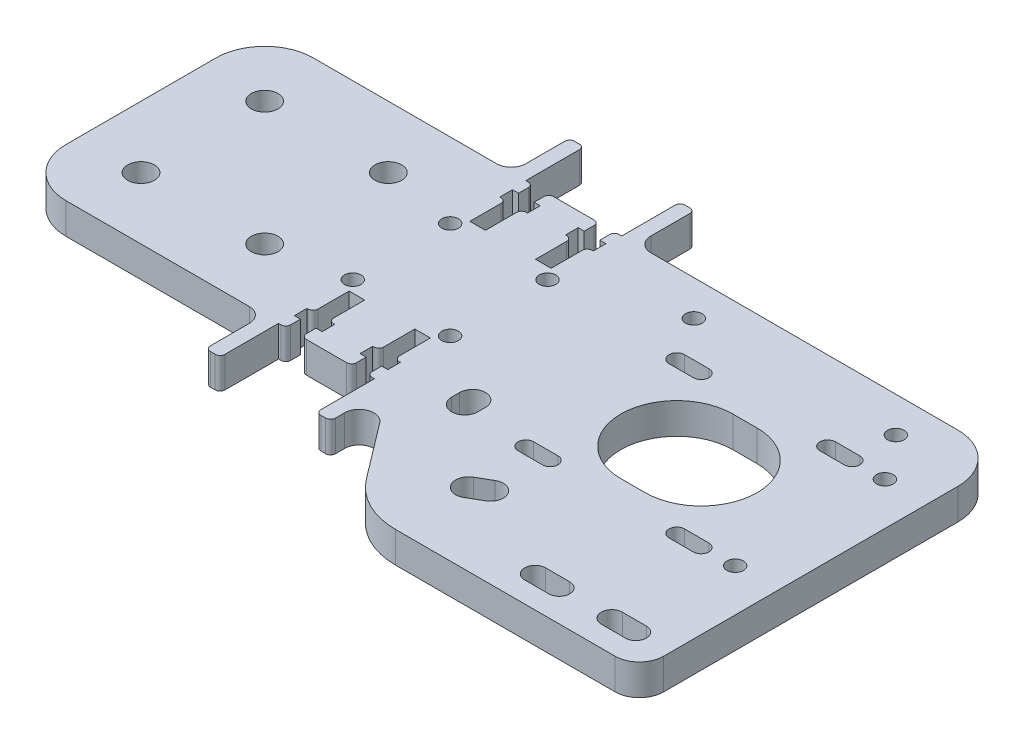
SolidWorks part; units mm, degrees
material "6061-T6 (SS)"
ref_plane "Front" through (0, 0, 0) normal (0, 0, 1) x (1, 0, 0)
ref_plane "Top" through (0, 0, 0) normal (0, 1, 0) x (1, 0, 0)
ref_plane "Right" through (0, 0, 0) normal (1, 0, 0) x (0, 0, -1)
sketch "Sketch1" plane through (0, 0, 0) normal (0, 1, 0) x (1, 0, 0)
  line L0 (0, 0) -> (114.3212, 0) construction
  line L1 (38.1, -25.4) -> (-38.1, -25.4)
  line L2 (38.1, -25.4) -> (38.1, 25.4) construction
  line L3 (38.1, 25.4) -> (-38.1, 25.4)
  line L4 (-38.1, -25.4) -> (-38.1, 25.4)
  line L5 (38.1, -25.4) -> (-38.1, 25.4) construction
  line L6 (38.1, 25.4) -> (-38.1, -25.4) construction
  line L7 (25.4, 25.4) -> (25.4, -25.4) construction
  line L8 (-25.4, 25.4) -> (-25.4, -25.4) construction
  line L9 (0, -25.4) -> (0, 25.4) construction
  line L10 (0, 0) -> (-38.1, 0) construction
  line L11 (-25.4, 0) -> (-25.4, 25.4) construction
  line L12 (-25.4, 12.7) -> (0, 12.7) construction
  line L13 (25.4, -41.4) -> (114.3212, -41.4) construction
  line L14 (99.3212, -27.36) -> (57.3212, -27.36) construction
  line L15 (99.3212, -27.36) -> (99.3212, 14.64) construction
  line L16 (99.3212, 14.64) -> (57.3212, 14.64) construction
  line L17 (57.3212, -27.36) -> (57.3212, 14.64) construction
  line L18 (99.3212, -27.36) -> (57.3212, 14.64) construction
  line L19 (99.3212, 14.64) -> (57.3212, -27.36) construction
  line L20 (93.8212, -21.86) -> (62.8212, -21.86) construction
  line L21 (93.8212, -21.86) -> (93.8212, 9.14) construction
  line L22 (93.8212, 9.14) -> (62.8212, 9.14) construction
  line L23 (62.8212, -21.86) -> (62.8212, 9.14) construction
  line L24 (93.8212, -21.86) -> (62.8212, 9.14) construction
  line L25 (93.8212, 9.14) -> (62.8212, -21.86) construction
  line L26 (114.3212, -41.4) -> (114.3212, 0) construction
  line L27 (49.1, -12.72) -> (78.3212, -12.72) construction
  line L28 (47.8664, -25.3192) -> (65.4755, -28.8008) construction
  line L29 (38.1, -25.4) -> (52.2919, -44.1062)
  line L30 (78.3212, 0) -> (0, 0) construction
  line L31 (35.4, 10) -> (15.4, 10) construction
  line L32 (64.2419, -50.04) -> (114.3212, -50.04)
  line L33 (114.3212, -50.04) -> (114.3212, 25.4)
  line L34 (114.3212, 25.4) -> (38.1, 25.4)
  line L35 (49.1, -19.08) -> (49.1, -20.72) construction
  line L36 (64.2419, -35.04) -> (67.0783, -33.4) construction
  line L37 (64.2419, -35.04) -> (64.2419, -50.04) construction
  circle A0 centre (-25.4, 12.7) radius 2.5 construction
  circle A1 centre (0, 12.7) radius 2.5 construction
  circle A2 centre (-25.4, -12.7) radius 2.5 construction
  circle A3 centre (0, -12.7) radius 2.5 construction
  circle A4 centre (78.3212, -6.36) radius 6.36 construction
  circle A5 centre (78.3212, -6.36) radius 11 construction
  circle A6 centre (62.8212, 9.14) radius 1.5 construction
  circle A7 centre (93.8212, 9.14) radius 1.5 construction
  circle A8 centre (93.8212, -21.86) radius 1.5 construction
  circle A9 centre (62.8212, -21.86) radius 1.5 construction
  circle A10 centre (64.2419, -35.04) radius 6.36 construction
  circle A11 centre (64.2419, -35.04) radius 11 construction
  circle A12 centre (49.1, -19.08) radius 6.36 construction
  circle A13 centre (49.1, -19.08) radius 11 construction
  circle A14 centre (62.8212, -21.86) radius 3 construction
  circle A15 centre (35.4, 10) radius 1.5 construction
  circle A16 centre (15.4, 10) radius 1.5 construction
  circle A17 centre (35.4, -10) radius 1.5 construction
  circle A18 centre (15.4, -10) radius 1.5 construction
  circle A19 centre (49.1, -19.08) radius 2.5 construction
  circle A20 centre (64.2419, -35.04) radius 2.5 construction
  circle A21 centre (78.3212, -6.36) radius 11 construction
  arc A22 (52.2919, -44.1062) -> (64.2419, -50.04) centre (64.2419, -35.04) ccw
  circle A23 centre (49.1, -20.72) radius 8 construction
  circle A24 centre (49.1, -20.72) radius 11 construction
  circle A25 centre (67.0783, -33.4) radius 8 construction
  circle A26 centre (67.0783, -33.4) radius 11 construction
  point P0 (0, 0)
  point P54 (25.4, 10)
  dimension "D6" = 5
  dimension "D7" = 12.72
  dimension "D9" = 22
  dimension "D11" = 3
  dimension "D12" = 16
  dimension "D13" = 6
  dimension "D16" = 3
  dimension "D17" = 5
  dimension "D18" = 22
  dimension "D20" = 16
  dimension "D21" = 4
  dimension "D1" = 50.8
  dimension "D2" = 76.2
  dimension "D3" = 12.7
  dimension "D4" = 12.7
  dimension "D5" = 25.4
  dimension "D8" = 42
  dimension "D10" = 31
  dimension "D14" = 20
  dimension "D15" = 10
  dimension "D19" = 15
extrude "Boss-Extrude1" add sketch "Sketch1" along normal blind 6.35
hole_wizard "M5 Clearance Hole1" positions "Sketch3" profile "Sketch2" hole size "M5" standard "ISO" end condition through all
sketch "Sketch3" plane through (0, 6.35, 0) normal (0, 1, 0) x (1, 0, 0)
  point P0 (-25.4, 12.7)
  point P3 (0, 12.7)
  point P6 (0, -12.7)
  point P9 (-25.4, -12.7)
sketch "Sketch2" plane through (-25.4, 6.35, -12.7) normal (1, 0, 0) x (0, 0, 1)
  line L0 (0, 0) -> (0, 6.35)
  line L1 (0, 6.35) -> (2.75, 6.35)
  line L2 (2.75, 6.35) -> (2.75, 0)
  line L5 (2.75, 0) -> (0, 0)
  line L11 (0, -6.35) -> (0, 107.95) construction
  dimension "Thru Hole Dia." = 5.5
  dimension "Thru Hole Depth" = 6.35
hole_wizard "M3 Clearance Hole1" positions "Sketch5" profile "Sketch4" hole size "M3" standard "ISO" end condition through all
sketch "Sketch5" plane through (0, 6.35, 0) normal (0, 1, 0) x (1, 0, 0)
  point P0 (15.4, 10)
  point P3 (35.4, 10)
  point P6 (35.4, -10)
  point P9 (15.4, -10)
sketch "Sketch4" plane through (15.4, 6.35, -10) normal (1, 0, 0) x (0, 0, 1)
  line L0 (0, 0) -> (0, 6.35)
  line L1 (0, 6.35) -> (1.7, 6.35)
  line L2 (1.7, 6.35) -> (1.7, 0)
  line L5 (1.7, 0) -> (0, 0)
  line L11 (0, -6.35) -> (0, 107.95) construction
  dimension "Thru Hole Dia." = 3.4
  dimension "Thru Hole Depth" = 6.35
sketch "Sketch6" plane through (0, 6.35, 0) normal (0, 1, 0) x (1, 0, 0)
  line L0 (62.8212, 9.14) -> (67.8212, 9.14) construction
  line L1 (93.8212, 9.14) -> (62.8212, 9.14) construction
  line L2 (62.8212, -21.86) -> (67.8212, -21.86) construction
  line L3 (93.8212, -21.86) -> (62.8212, -21.86) construction
  line L4 (93.8212, -21.86) -> (98.8212, -21.86) construction
  line L5 (93.8212, 9.14) -> (98.8212, 9.14) construction
  line L6 (62.8212, 7.54) -> (67.8212, 7.54)
  line L7 (62.8212, -23.46) -> (67.8212, -23.46)
  line L8 (93.8212, -23.46) -> (98.8212, -23.46)
  line L9 (93.8212, 7.54) -> (98.8212, 7.54)
  line L10 (62.8212, 10.74) -> (67.8212, 10.74)
  line L11 (62.8212, -20.26) -> (67.8212, -20.26)
  line L12 (93.8212, -20.26) -> (98.8212, -20.26)
  line L13 (93.8212, 10.74) -> (98.8212, 10.74)
  line L14 (78.3212, -6.36) -> (83.3212, -6.36) construction
  line L15 (99.3212, 14.64) -> (57.3212, -27.36) construction
  line L16 (78.3212, -17.86) -> (83.3212, -17.86)
  line L17 (78.3212, 5.14) -> (83.3212, 5.14)
  arc A0 (62.8212, 7.54) -> (62.8212, 10.74) centre (62.8212, 9.14) cw
  arc A1 (67.8212, 7.54) -> (67.8212, 10.74) centre (67.8212, 9.14) ccw
  arc A2 (62.8212, -23.46) -> (62.8212, -20.26) centre (62.8212, -21.86) cw
  arc A3 (67.8212, -23.46) -> (67.8212, -20.26) centre (67.8212, -21.86) ccw
  arc A4 (93.8212, -23.46) -> (93.8212, -20.26) centre (93.8212, -21.86) cw
  arc A5 (98.8212, -23.46) -> (98.8212, -20.26) centre (98.8212, -21.86) ccw
  arc A6 (93.8212, 7.54) -> (93.8212, 10.74) centre (93.8212, 9.14) cw
  arc A7 (98.8212, 7.54) -> (98.8212, 10.74) centre (98.8212, 9.14) ccw
  arc A8 (78.3212, -17.86) -> (78.3212, 5.14) centre (78.3212, -6.36) cw
  arc A9 (83.3212, -17.86) -> (83.3212, 5.14) centre (83.3212, -6.36) ccw
  dimension "D1" = 5
  dimension "D2" = 1.6
  dimension "D3" = 1.6
  dimension "D4" = 11.5
  dimension "D5" = 11.5
extrude "Cut-Extrude1" cut sketch "Sketch6" against normal through all
sketch "Sketch7" plane through (0, 6.35, 0) normal (0, 1, 0) x (1, 0, 0)
  line L0 (49.1, -19.08) -> (49.1, -20.72) construction
  line L1 (67.0783, -33.4) -> (64.2419, -35.04) construction
  line L2 (65.7518, -31.1059) -> (62.9155, -32.7459)
  line L3 (46.45, -19.08) -> (46.45, -20.72)
  line L4 (68.4047, -35.6941) -> (65.5684, -37.3341)
  line L5 (51.75, -19.08) -> (51.75, -20.72)
  arc A0 (65.7518, -31.1059) -> (68.4047, -35.6941) centre (67.0783, -33.4) cw
  arc A1 (62.9155, -32.7459) -> (65.5684, -37.3341) centre (64.2419, -35.04) ccw
  arc A2 (46.45, -19.08) -> (51.75, -19.08) centre (49.1, -19.08) cw
  arc A3 (46.45, -20.72) -> (51.75, -20.72) centre (49.1, -20.72) ccw
  dimension "D1" = 2.65
  dimension "D2" = 2.65
extrude "Cut-Extrude2" cut sketch "Sketch7" against normal through all
fillet "Fillet1" radius 10 3 edges at (114.3212, 3.175, -25.4) (-38.1, 3.175, -25.4) (-38.1, 3.175, 25.4)
sketch "Sketch8" plane through (0, 6.35, 0) normal (0, 1, 0) x (1, 0, 0)
  line L0 (114.3212, -43.61) -> (79.3212, -43.61) construction
  line L1 (114.3212, -50.04) -> (114.3212, 15.4) construction
  line L2 (89.0712, -43.61) -> (104.5712, -43.61) construction
  line L3 (96.8212, -43.61) -> (96.8212, -25.11) construction
  line L4 (114.3212, -25.11) -> (79.3212, -25.11) construction
  line L5 (79.3212, -25.11) -> (79.3212, -57.11) construction
  line L6 (79.3212, -57.11) -> (114.3212, -57.11) construction
  line L7 (114.3212, -57.11) -> (114.3212, -25.11) construction
  line L8 (107.1712, -41.46) -> (102.2212, -41.46)
  line L9 (86.4712, -43.61) -> (91.4212, -43.61) construction
  line L10 (86.4712, -45.76) -> (91.4212, -45.76)
  line L11 (86.4712, -41.46) -> (91.4212, -41.46)
  line L12 (84.3212, -43.61) -> (84.3212, -50.04) construction
  line L13 (64.2419, -50.04) -> (114.3212, -50.04) construction
  line L14 (93.5712, -43.61) -> (93.5712, -50.04) construction
  line L15 (107.1712, -45.76) -> (102.2212, -45.76)
  circle A0 centre (104.5712, -43.61) radius 2 construction
  circle A1 centre (89.0712, -43.61) radius 2 construction
  arc A2 (86.4712, -45.76) -> (86.4712, -41.46) centre (86.4712, -43.61) cw
  arc A3 (91.4212, -45.76) -> (91.4212, -41.46) centre (91.4212, -43.61) ccw
  circle A4 centre (93.8212, -21.86) radius 3.25 construction
  circle A5 centre (67.0783, -33.4) radius 11 construction
  arc A6 (107.1712, -41.46) -> (107.1712, -45.76) centre (107.1712, -43.61) cw
  arc A7 (102.2212, -41.46) -> (102.2212, -45.76) centre (102.2212, -43.61) ccw
  point P13 (96.8212, -25.11)
  dimension "D3" = 4
  dimension "D11" = 6.5
  dimension "D12" = 22
  dimension "D2" = 15.5
  dimension "D4" = 18.5
  dimension "D5" = 32
  dimension "D8" = 25
  dimension "D9" = 6.5
  dimension "D10" = 35
  dimension "D6" = 2.15
  dimension "D7" = 2.15
extrude "Cut-Extrude3" cut sketch "Sketch8" against normal through all
sketch "Sketch10" plane through (0, 6.35, 0) normal (0, 1, 0) x (1, 0, 0)
  line L0 (114.3212, -25.11) -> (79.3212, -25.11) construction
  line L1 (57.3212, 14.64) -> (57.3212, 18.14) construction
  line L2 (57.3212, 18.14) -> (98.8212, 18.14) construction
  line L3 (98.8212, 18.14) -> (98.8212, 9.14) construction
  line L4 (98.8212, 9.14) -> (105.5666, 9.14) construction
  line L5 (105.5666, 9.14) -> (105.5666, -21.61) construction
  line L7 (99.3212, 14.64) -> (57.3212, 14.64) construction
  circle A0 centre (105.5666, -21.61) radius 3.5
  circle A1 centre (98.8212, -21.86) radius 3.25 construction
  circle A2 centre (98.8212, 9.14) radius 3.25 construction
  circle A3 centre (105.5666, 9.14) radius 3.5
  circle A4 centre (98.8212, 18.14) radius 3.5
  circle A5 centre (57.3212, 18.14) radius 3.5
  dimension "D1" = 6.5
  dimension "D2" = 7
hole_wizard "M3 Clearance Hole2" positions "Sketch12" profile "Sketch11" hole size "M3" standard "ISO" end condition through all
sketch "Sketch12" plane through (0, 6.35, 0) normal (0, 1, 0) x (1, 0, 0)
  point P0 (57.3212, 18.14)
  point P3 (98.8212, 18.14)
  point P6 (105.5666, 9.14)
  point P9 (105.5666, -21.61)
sketch "Sketch11" plane through (57.3212, 6.35, -18.14) normal (1, 0, 0) x (0, 0, 1)
  line L0 (0, 0) -> (0, 6.35)
  line L1 (0, 6.35) -> (1.7, 6.35)
  line L2 (1.7, 6.35) -> (1.7, 0)
  line L5 (1.7, 0) -> (0, 0)
  line L11 (0, -6.35) -> (0, 107.95) construction
  dimension "Thru Hole Dia." = 3.4
  dimension "Thru Hole Depth" = 6.35
fillet "Fillet3" radius 5 1 edges at (114.3212, 3.175, 50.04)
sketch "Sketch13" plane through (0, 6.35, 0) normal (0, 1, 0) x (1, 0, 0)
  line L0 (25.4, 25.4) -> (25.4, -25.4) construction
  line L1 (38.1, 25.4) -> (-38.1, 25.4) construction
  line L2 (35.25, 25.4) -> (38.25, 25.4)
  line L3 (35.25, 25.4) -> (35.25, 37.4)
  line L4 (35.25, 37.4) -> (38.25, 37.4)
  line L5 (38.25, 25.4) -> (38.25, 37.4)
  line L6 (12.55, 25.4) -> (12.55, 37.4)
  line L7 (15.55, 37.4) -> (12.55, 37.4)
  line L8 (15.55, 25.4) -> (15.55, 37.4)
  line L9 (15.55, 25.4) -> (12.55, 25.4)
  line L10 (0, 0) -> (38.1, 0) construction
  line L11 (38.1, -25.4) -> (38.1, 25.4) construction
  line L12 (15.55, -25.4) -> (12.55, -25.4)
  line L13 (15.55, -25.4) -> (15.55, -37.4)
  line L14 (15.55, -37.4) -> (12.55, -37.4)
  line L15 (12.55, -25.4) -> (12.55, -37.4)
  line L16 (38.25, -25.4) -> (38.25, -37.4)
  line L17 (35.25, -37.4) -> (38.25, -37.4)
  line L18 (35.25, -25.4) -> (35.25, -37.4)
  line L19 (35.25, -25.4) -> (38.25, -25.4)
  dimension "D1" = 12
  dimension "D2" = 3
  dimension "D3" = 19.7
extrude "Boss-Extrude2" add sketch "Sketch13" against normal up to surface (6.35 mm away) up to face at (57.3212, 0, -16.44)
fillet "Fillet4" radius 3 4 edges at (38.25, 3.175, -25.4) (12.55, 3.175, -25.4) (12.55, 3.175, 25.4) (38.25, 3.175, 25.5977)
sketch "Sketch14" plane through (0, 6.35, 0) normal (0, 1, 0) x (1, 0, 0)
  line L0 (25.4, 25.4) -> (25.4, -25.4) construction
  line L1 (0, 0) -> (38.1, 0) construction
  line L2 (38.1, -25.4) -> (38.1, 25.4) construction
  line L3 (18.65, 25.4) -> (18.65, 12.4) construction
  line L4 (38.1, 25.4) -> (-38.1, 25.4) construction
  line L5 (17.05, 12.4) -> (20.25, 12.4)
  line L6 (20.25, 12.4) -> (20.25, 19.8)
  line L7 (20.25, 19.8) -> (21.5, 19.8)
  line L8 (21.5, 19.8) -> (21.5, 22.4)
  line L9 (21.5, 22.4) -> (20.25, 22.4)
  line L10 (20.25, 22.4) -> (20.25, 25.4)
  line L11 (20.25, 25.4) -> (17.05, 25.4)
  line L12 (17.05, 22.4) -> (17.05, 25.4)
  line L13 (15.8, 22.4) -> (17.05, 22.4)
  line L14 (15.8, 19.8) -> (15.8, 22.4)
  line L15 (17.05, 19.8) -> (15.8, 19.8)
  line L16 (17.05, 12.4) -> (17.05, 19.8)
  line L17 (35, 22.4) -> (33.75, 22.4)
  line L18 (35, 19.8) -> (35, 22.4)
  line L19 (33.75, 19.8) -> (35, 19.8)
  line L20 (33.75, 12.4) -> (33.75, 19.8)
  line L21 (33.75, 12.4) -> (30.55, 12.4)
  line L22 (30.55, 12.4) -> (30.55, 19.8)
  line L23 (30.55, 19.8) -> (29.3, 19.8)
  line L24 (29.3, 19.8) -> (29.3, 22.4)
  line L25 (29.3, 22.4) -> (30.55, 22.4)
  line L26 (30.55, 22.4) -> (30.55, 25.4)
  line L27 (30.55, 25.4) -> (33.75, 25.4)
  line L28 (33.75, 22.4) -> (33.75, 25.4)
  line L29 (21.5, -22.4) -> (20.25, -22.4)
  line L30 (21.5, -19.8) -> (21.5, -22.4)
  line L31 (20.25, -19.8) -> (21.5, -19.8)
  line L32 (20.25, -12.4) -> (20.25, -19.8)
  line L33 (17.05, -12.4) -> (20.25, -12.4)
  line L34 (17.05, -12.4) -> (17.05, -19.8)
  line L35 (17.05, -19.8) -> (15.8, -19.8)
  line L36 (15.8, -19.8) -> (15.8, -22.4)
  line L37 (15.8, -22.4) -> (17.05, -22.4)
  line L38 (17.05, -22.4) -> (17.05, -25.4)
  line L39 (20.25, -25.4) -> (17.05, -25.4)
  line L40 (20.25, -22.4) -> (20.25, -25.4)
  line L41 (30.55, -19.8) -> (29.3, -19.8)
  line L42 (30.55, -12.4) -> (30.55, -19.8)
  line L43 (33.75, -12.4) -> (30.55, -12.4)
  line L44 (33.75, -12.4) -> (33.75, -19.8)
  line L45 (33.75, -19.8) -> (35, -19.8)
  line L46 (35, -19.8) -> (35, -22.4)
  line L47 (35, -22.4) -> (33.75, -22.4)
  line L48 (33.75, -22.4) -> (33.75, -25.4)
  line L49 (30.55, -25.4) -> (33.75, -25.4)
  line L50 (30.55, -22.4) -> (30.55, -25.4)
  line L51 (29.3, -22.4) -> (30.55, -22.4)
  line L52 (29.3, -19.8) -> (29.3, -22.4)
  dimension "D1" = 5.7
  dimension "D2" = 2.6
  dimension "D3" = 3
  dimension "D4" = 3.2
  dimension "D5" = 13.5
  dimension "D6" = 13
extrude "Cut-Extrude4" cut sketch "Sketch14" against normal through all
fillet "Fillet5" radius 1 16 edges at (35.25, 3.175, -37.4) (15.55, 3.175, -37.4) (35.25, 3.175, 37.4) (15.55, 3.175, 37.4) (12.55, 3.175, -37.4) (38.25, 3.175, -37.4) (38.25, 3.175, 37.4) (12.55, 3.175, 37.4) (33.75, 3.175, 25.4) (17.05, 3.175, 25.4) (17.05, 3.175, 19.8) (20.25, 3.175, 19.8) (33.75, 3.175, 19.8) (30.55, 3.175, 19.8) (30.55, 3.175, 25.4) (20.25, 3.175, 25.4)
fillet "Fillet6" radius 1 8 edges at (33.75, 3.175, -19.8) (30.55, 3.175, -19.8) (20.25, 3.175, -19.8) (17.05, 3.175, -19.8) (17.05, 3.175, -25.4) (20.25, 3.175, -25.4) (33.75, 3.175, -25.4) (30.55, 3.175, -25.4)
